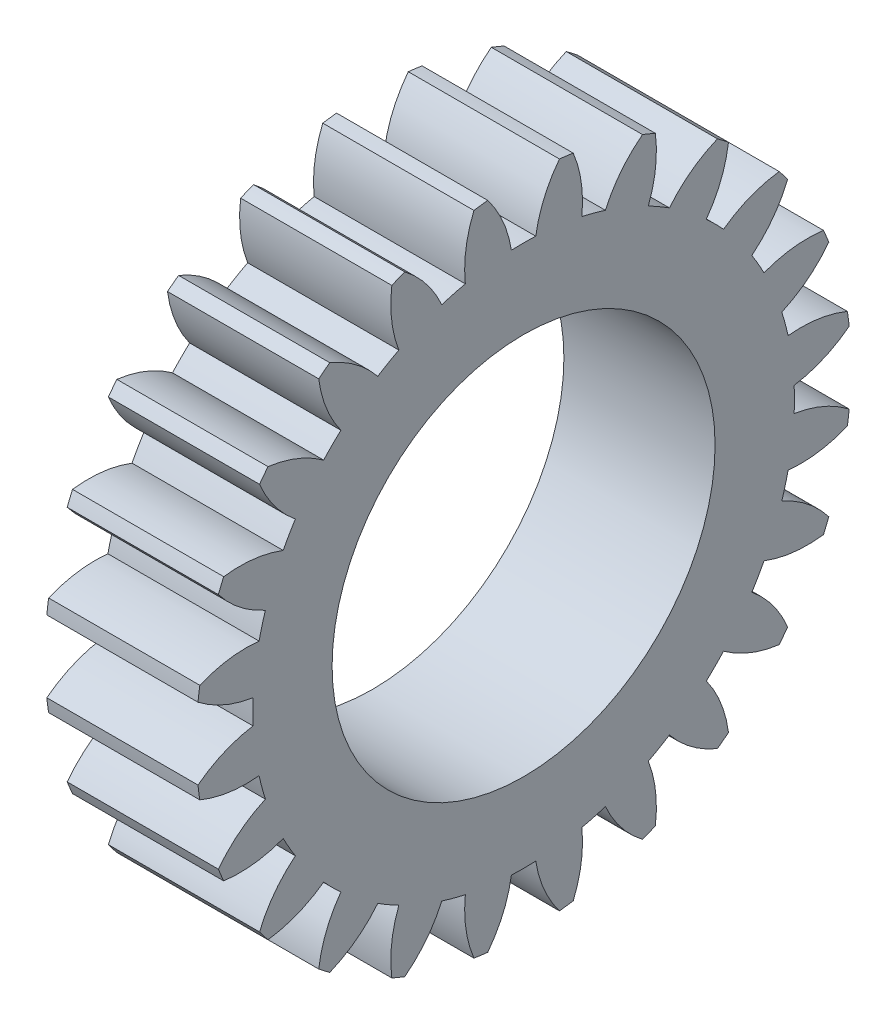
SolidWorks part; units mm, degrees
ref_plane "Plane1" through (0, 0, 0) normal (0, 0, 1) x (1, 0, 0)
ref_plane "Plane2" through (0, 0, 0) normal (0, 1, 0) x (1, 0, 0)
ref_plane "Plane3" through (0, 0, 0) normal (1, 0, 0) x (0, 0, -1)
other "Configuration Table"
sketch "HoldingSke" plane through (0, 0, 0) normal (0, 1, 0) x (1, 0, 0)
  line L0 (0, 0) -> (0.9135, -0.4067)
  line L1 (-15, 0) -> (100, 0) construction
  line L2 (0, 0) -> (-2.1039, 2.3779)
  line L3 (0, 0) -> (-11.863, 4.5341)
  line L4 (0, 0) -> (7.8894, 3.5126)
  line L5 (0, 0) -> (-46.8476, -17.4728)
  line L6 (0, 0) -> (-4.9738, -3.3558)
  line L7 (-2.1039, 2.3779) -> (8.6586, 51.2059)
  line L8 (-76.2, 54.61) -> (-75.5, 54.61)
  line L9 (-71.009, 38.7566) -> (-53.1078, 45.2721)
  line L10 (-76.2, 71.12) -> (104.1128, 71.12)
  line L11 (0, 0) -> (-6, 0)
  line L12 (-76.2, 101.6) -> (-76.162, 101.6)
  line L13 (24.9733, 27.94) -> (52.9518, 28.4284)
  line L14 (24.9733, 27.94) -> (24.9743, 27.94)
  line L15 (24.9733, 27.94) -> (100.4006, 29.5858)
  line L16 (-63.627, -1) -> (-12.827, -1)
  circle A0 centre (0, 0) radius 7.6
  circle A1 centre (0, 0) radius 10.749
  circle A2 centre (0, 0) radius 37.5
  circle A3 centre (0, 0) radius 7.6
  dimension "MHD" = 21.498
  dimension "Hub_dia" = 75
  dimension "Bore" = 15.2
  dimension "MBD" = 15.2
  dimension "Num_teeth" = 24
  dimension "Pitch" = 1
  dimension "Overall_len" = 50
  dimension "Show_teeth" = 24
  dimension "Thickness" = 6
  dimension "OAL" = 50.0001
  dimension "T_dim" = 0.7
  dimension "Ap" = 20
  dimension "H" = 19.05
  dimension "Pitch_radius" = 180.3128
  dimension "Width" = 6
  dimension "Backlash" = 0.038
  dimension "Addendum_fac" = 1
  dimension "Dedendum_fac" = 1.25
  dimension "Clearance_fac" = 0.25
  dimension "Dedendum_add" = 0.001
  dimension "Module" = 1
sketch "BasProSke" plane through (0, 0, 0) normal (0, 1, 0) x (1, 0, 0)
  line L0 (-10, 0) -> (60, 0) construction
  line L1 (0, 0) -> (0, 13)
  line L2 (0, 0) -> (6, 0)
  line L3 (6, 0) -> (6, 13)
  line L4 (6, 13) -> (0, 13)
  dimension "Thickness" = 6
  dimension "Diameter" = 26
revolve "Base-Revolve" add sketch "BasProSke" angle 360 about L0
sketch "TooCutSke" plane through (0, 0, 0) normal (1, 0, 0) x (0, 0, -1)
  line L1 (0, 0) -> (0, 107) construction
  line L2 (0, 0) -> (-0.8513, 11.9698) construction
  line L3 (0, 0) -> (-3.127, 23.752) construction
  line L4 (-0.8513, 11.9698) -> (-1.5635, 11.876) construction
  arc A0 (0.4834, 10.7381) -> (-0.4834, 10.7381) centre (0, 0) ccw
  arc A1 (1.4409, 12.9455) -> (-1.4409, 12.9455) centre (0, 0) ccw
  circle A2 centre (0, 0) radius 12 construction
  circle A3 centre (0, 0) radius 11.2763 construction
  arc A4 (-0.4834, 10.7381) -> (-1.4409, 12.9455) centre (-5.2252, 9.9926) ccw
  arc A5 (1.4409, 12.9455) -> (0.4834, 10.7381) centre (5.2252, 9.9926) ccw
  dimension "Root_dia" = 21.498
  dimension "Overcut_dia" = 26.0508
  dimension "Pitch_dia" = 24
  dimension "Base_dia" = 22.5526
  dimension "Flank_rad" = 4.8
  dimension "Half_ang" = 7.5
  dimension "Half_CT" = 0.7183
extrude "ToothCut" cut sketch "TooCutSke" along normal through all
fillet "Breaks" [suppressed] radius 0.02
fillet "RootFillets" [suppressed] radius 0.251
pattern_circular "TeethCuts" count 24 every 15 about axis through (-10, 0, 0) along (1, 0, 0) of "ToothCut", "RootFillets", "Breaks"
sketch "HubNeaOneSke" plane through (0, 0, 0) normal (-1, 0, 0) x (0, 0, 1)
  circle A0 centre (0, 0) radius 10.749
  dimension "Diameter" = 21.498
extrude "HubNearOne" [suppressed] add sketch "HubNeaOneSke" along normal blind 44.0001
sketch "HubNeaBotSke" plane through (0, 0, 0) normal (-1, 0, 0) x (0, 0, 1)
  circle A0 centre (0, 0) radius 10.749
  dimension "Diameter" = 21.498
extrude "HubNearBoth" [suppressed] add sketch "HubNeaBotSke" along normal blind 22
ref_plane "FarPln" through (6, 0, 0) normal (1, 0, 0) x (0, 0, -1)
sketch "HubFarSke" plane through (6, 0, 0) normal (1, 0, 0) x (0, 0, -1)
  circle A0 centre (0, 0) radius 10.749
  dimension "Diameter" = 21.498
extrude "HubFar" [suppressed] add sketch "HubFarSke" along normal blind 22
sketch "BorSke" plane through (0, 0, 0) normal (1, 0, 0) x (0, 0, -1)
  circle A0 centre (0, 0) radius 7.6
  dimension "Diameter" = 15.2
extrude "Bore" cut sketch "BorSke" along normal mid plane 100.0001
sketch "KeySke" plane through (0, 0, 0) normal (1, 0, 0) x (0, 0, -1)
  line L0 (-0.8, 0) -> (-0.8, 8.3)
  line L1 (-0.8, 8.3) -> (0.8, 8.3)
  line L2 (0.8, 8.3) -> (0.8, 0)
  line L3 (0, 0) -> (0, 34) construction
  line L4 (-0.8, 0) -> (0.8, 0)
  dimension "Offset" = 8.3
  dimension "Width" = 1.6
extrude "Keyway" [suppressed] cut sketch "KeySke" along normal mid plane 100.0001
pattern_circular "Keyway2" [suppressed] count 2 every 90 about axis through (-10, 0, 0) along (1, 0, 0)
equation "' \"Module@HoldingSke\" = 6.35"
equation "' \"Num_teeth@HoldingSke\" = 12"
equation "' \"Ap@HoldingSke\" =  20"
equation "' \"Ap@HoldingSke\" = 20"
equation "' \"Width@HoldingSke\" = 0.5 * 25.4"
equation "' \"Hub_dia@HoldingSke\"= 1 * 25.4"
equation "' \"Hub_dia@HoldingSke\" = 1 * 25.4"
equation "' \"Overall_len@HoldingSke\" = 1.0 * 25.4"
equation "' \"Bore@HoldingSke\" = 0.75 * 25.4"
equation "' \"T_dim@HoldingSke\" = 0.1 * 25.4"
equation "' \"Width@KeySke\" = 0.25 * 25.4"
equation "' \"Show_teeth@HoldingSke\" = 13"
equation "' \"Backlash@HoldingSke\" = 0.009 * 25.4"
equation "' \"Addendum_fac@HoldingSke\" = 1.0"
equation "' \"Dedendum_fac@HoldingSke\" = 1.25"
equation "' \"Dedendum_add@HoldingSke\" = 0.00005 * 25.4"
equation "' \"Clearance_fac@HoldingSke\" = 0.25"
equation "\"Pitch@HoldingSke\" = 1 / \"Module@HoldingSke\""
equation "\"Overcut_dia@TooCutSke\" = (\"Num_teeth@HoldingSke\" + 2 * \"Addendum_fac@HoldingSke\") / \"Pitch@HoldingSke\" + 0.002 * 25.4"
equation "\"Pitch_dia@TooCutSke\" = \"Num_teeth@HoldingSke\" / \"Pitch@HoldingSke\""
equation "\"Base_dia@TooCutSke\" = \"Num_teeth@HoldingSke\" / \"Pitch@HoldingSke\" * cos((\"Ap@HoldingSke\"  * 3.14159265 / 180))"
equation "\"Root_dia@TooCutSke\" = (\"Num_teeth@HoldingSke\" + 2) / \"Pitch@HoldingSke\" - 2 * (\"Addendum_fac@HoldingSke\" + \"Dedendum_fac@HoldingSke\") / \"Pitch@HoldingSke\" - \"Dedendum_add@HoldingSke\" * 2"
equation "\"Half_ang@TooCutSke\" = 180 / \"Num_teeth@HoldingSke\""
equation "\"Half_CT@TooCutSke\" = \"Num_teeth@HoldingSke\" / \"Pitch@HoldingSke\" * sin((3.14159265 / 2 / \"Num_teeth@HoldingSke\")) / 2 - 7 * \"Backlash@HoldingSke\" / 4"
equation "\"Flank_rad@TooCutSke\" = \"Num_teeth@HoldingSke\" / \"Pitch@HoldingSke\" / 5"
equation "\"Radius@RootFillets\" = \"Clearance_fac@HoldingSke\" / \"Pitch@HoldingSke\" + \"Dedendum_add@HoldingSke\""
equation "\"Break_rad@Breaks\" = 0.02 / \"Pitch@HoldingSke\""
equation "\"Thickness@HoldingSke\" = \"Width@HoldingSke\""
equation "\"OAL@HoldingSke\" = \"Thickness@HoldingSke\""
equation "\"MHD@HoldingSke\" = (\"Num_teeth@HoldingSke\" + 2) / \"Pitch@HoldingSke\" - 2 * (\"Addendum_fac@HoldingSke\" + \"Dedendum_fac@HoldingSke\")  / \"Pitch@HoldingSke\" - \"Dedendum_add@HoldingSke\" * 2"
equation "\"MBD@HoldingSke\" = (\"Num_teeth@HoldingSke\" + 2) / \"Pitch@HoldingSke\" - 2 * (\"Addendum_fac@HoldingSke\" + \"Dedendum_fac@HoldingSke\")  / \"Pitch@HoldingSke\" - \"Dedendum_add@HoldingSke\" * 2 - 0.002 * 25.4"
equation "\"MHD@HoldingSke\" = ((sgn( \"MHD@HoldingSke\" - \"Hub_dia@HoldingSke\" )-1)*( \"MHD@HoldingSke\" - \"Hub_dia@HoldingSke\" ))/-2+ \"Hub_dia@HoldingSke\""
equation "\"MBD@HoldingSke\" = ((sgn( \"MBD@HoldingSke\" - \"Bore@HoldingSke\" )-1)*( \"MBD@HoldingSke\" - \"Bore@HoldingSke\" ))/-2+ \"Bore@HoldingSke\""
equation "\"OAL@HoldingSke\" = ((sgn( \"OAL@HoldingSke\" - \"Overall_len@HoldingSke\" )+1)*( \"OAL@HoldingSke\" - \"Overall_len@HoldingSke\" ))/2 + \"Overall_len@HoldingSke\" + 0.000002 * 25.4"
equation "\"Num_teeth@TeethCuts\" = int( \"Show_teeth@HoldingSke\" ) + 1"
equation "\"Num_teeth@TeethCuts\" = ((sgn( \"Num_teeth@TeethCuts\" - \"Num_teeth@HoldingSke\" )-1)*( \"Num_teeth@TeethCuts\" - \"Num_teeth@HoldingSke\" ))/-2+ \"Num_teeth@HoldingSke\""
equation "\"Num_teeth@TeethCuts\" = ((sgn( \"Num_teeth@TeethCuts\" - 2.0)+1)*( \"Num_teeth@TeethCuts\" - 2.0))/2 +2.0"
equation "\"Angle@TeethCuts\" = 360.0 / \"Num_teeth@HoldingSke\""
equation "\"Diameter@BasProSke\" = (\"Num_teeth@HoldingSke\" + 2 * \"Addendum_fac@HoldingSke\") / \"Pitch@HoldingSke\""
equation "\"Thickness@BasProSke\"  = \"Thickness@HoldingSke\""
equation "' \"Fillet_rad@BasProSke\" =  \"Thickness@HoldingSke\" * 0.05"
equation "' \"Fillet_rad@BasProSke\" = \"Thickness@HoldingSke\" * 0.05"
equation "\"MHD@HoldingSke\" = ((sgn( \"MHD@HoldingSke\" - \"Root_dia@TooCutSke\" )-1)*( \"MHD@HoldingSke\" - \"Root_dia@TooCutSke\" ))/-2+ \"Root_dia@TooCutSke\""
equation "\"Diameter@HubNeaOneSke\" = \"MHD@HoldingSke\""
equation "\"Length@HubNearOne\" = \"OAL@HoldingSke\" - \"Thickness@BasProSke\""
equation "\"Diameter@HubNeaBotSke\" = \"MHD@HoldingSke\""
equation "\"Length@HubNearBoth\" = ( \"OAL@HoldingSke\" - \"Thickness@BasProSke\" ) / 2.0"
equation "\"Thickness@FarPln\" = \"Thickness@BasProSke\""
equation "\"Diameter@HubFarSke\" = \"MHD@HoldingSke\""
equation "\"Length@HubFar\" = ( \"OAL@HoldingSke\" - \"Thickness@BasProSke\" ) / 2.0"
equation "\"Diameter@BorSke\" = \"MBD@HoldingSke\""
equation "\"D1@Bore\" = \"OAL@HoldingSke\" * 2.0"
equation "\"D1@Keyway\" = \"OAL@HoldingSke\" * 2.0"
equation "\"Offset@KeySke\" = \"T_dim@HoldingSke\" + \"MBD@HoldingSke\" / 2.0"
